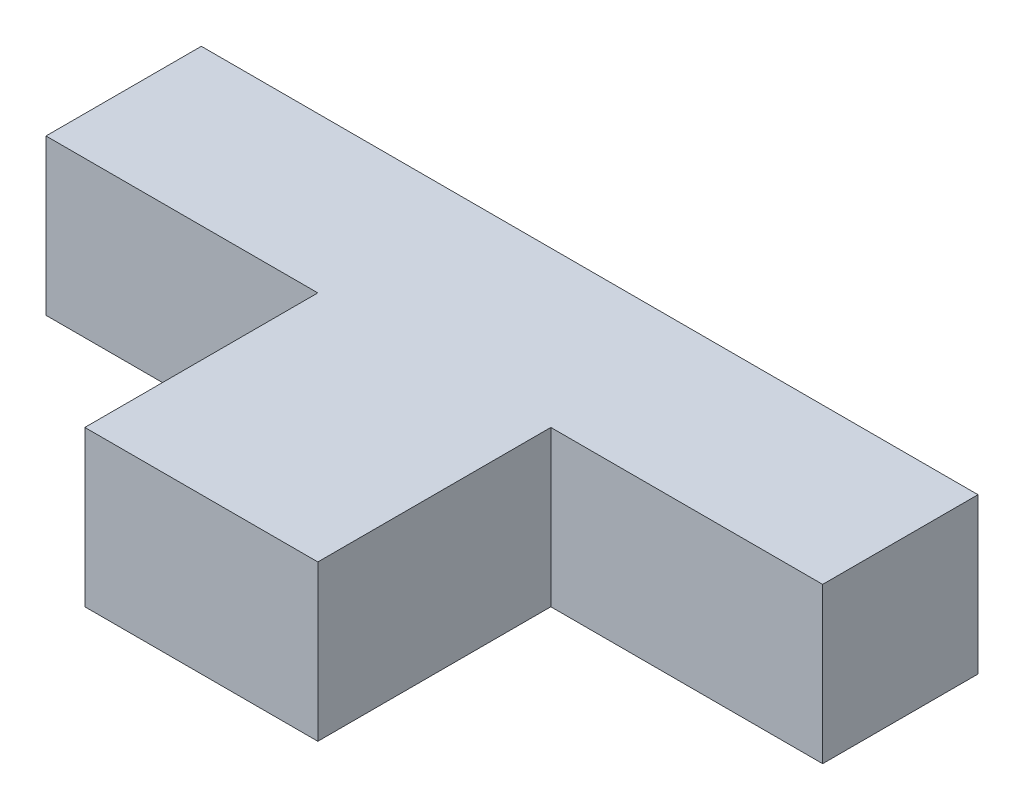
SolidWorks part; units mm, degrees
ref_plane "Front Plane" through (0, 0, 0) normal (0, 0, 1) x (1, 0, 0)
ref_plane "Top Plane" through (0, 0, 0) normal (0, 1, 0) x (1, 0, 0)
ref_plane "Right Plane" through (0, 0, 0) normal (1, 0, 0) x (0, 0, -1)
sketch "Sketch1" plane through (0, 0, 0) normal (0, 1, 0) x (1, 0, 0)
  line L1 (38.1, -50.8) -> (-38.1, -50.8)
  line L2 (38.1, -50.8) -> (38.1, 50.8)
  line L3 (38.1, 50.8) -> (-38.1, 50.8)
  line L4 (-38.1, -50.8) -> (-38.1, 50.8)
  line L5 (38.1, -50.8) -> (-38.1, 50.8) construction
  line L6 (38.1, 50.8) -> (-38.1, -50.8) construction
  line L7 (-127, 25.4) -> (127, 25.4)
  line L8 (-127, 25.4) -> (-127, 76.2)
  line L9 (-127, 76.2) -> (127, 76.2)
  line L10 (127, 25.4) -> (127, 76.2)
  line L11 (-127, 25.4) -> (127, 76.2) construction
  line L12 (-127, 76.2) -> (127, 25.4) construction
  point P0 (0, 0)
  point P5 (0, 50.8)
  point P10 (0, 0)
  dimension "D1" = 254
  dimension "D2" = 50.8
  dimension "D3" = 76.2
  dimension "D4" = 101.6
extrude "Boss-Extrude1" add sketch "Sketch1" along normal blind 50.8 contours L7 L10 L9 L8 L4 L3 L2 | L7 L4 L1 L2 | L4 L7 L2 L3
